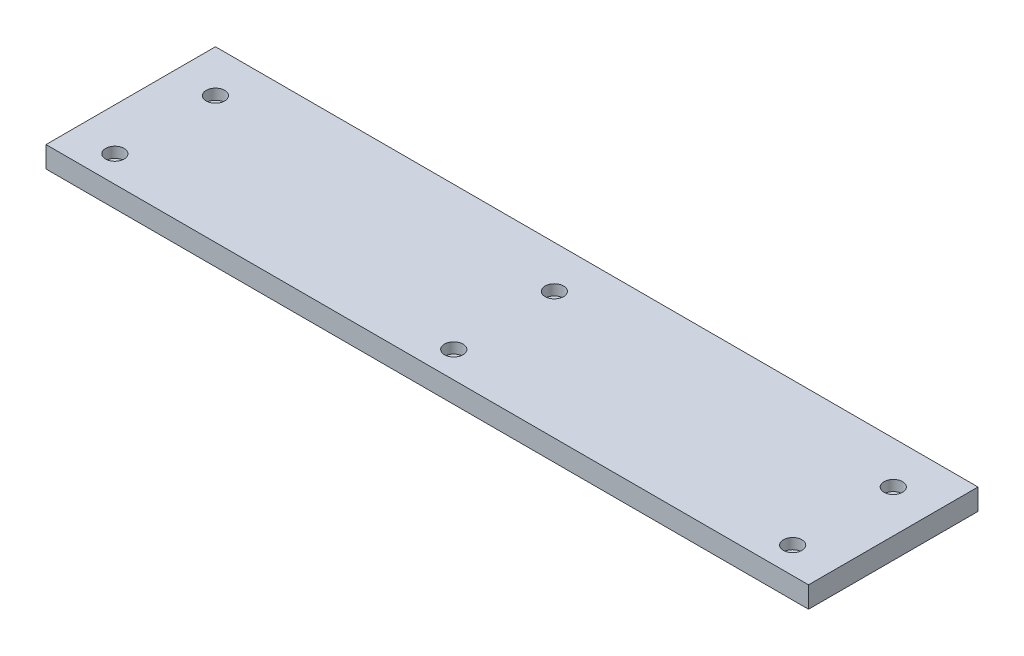
SolidWorks part; units mm, degrees
material "Ceramic Porcelain"
ref_plane "Front Plane" through (0, 0, 0) normal (0, 0, 1) x (1, 0, 0)
ref_plane "Top Plane" through (0, 0, 0) normal (0, 1, 0) x (1, 0, 0)
ref_plane "Right Plane" through (0, 0, 0) normal (1, 0, 0) x (0, 0, -1)
sketch "Sketch1" plane through (0, 0, 0) normal (0, 1, 0) x (1, 0, 0)
  line L1 (228.6, 50.8) -> (-228.6, 50.8)
  line L2 (228.6, 50.8) -> (228.6, -50.8)
  line L3 (228.6, -50.8) -> (-228.6, -50.8)
  line L4 (-228.6, 50.8) -> (-228.6, -50.8)
  line L5 (0, -50.8) -> (0, 50.8) construction
  line L6 (228.6, 0) -> (-228.6, 0) construction
  line L7 (203.2, -34.925) -> (-203.2, -34.925) construction
  line L8 (203.2, -34.925) -> (203.2, 25.4) construction
  line L9 (203.2, 25.4) -> (-203.2, 25.4) construction
  line L10 (-203.2, -34.925) -> (-203.2, 25.4) construction
  line L11 (0, 25.4) -> (0, -34.925) construction
  line L12 (203.2, -4.7625) -> (-203.2, -4.7625) construction
  point P0 (0, 0)
  point P4 (0, -4.7625)
  point P8 (0, 0)
  point P9 (0, 0)
  point P10 (0, 0)
  point P11 (0, 0)
  point P12 (0, 0)
  point P13 (0, 0)
  dimension "D1" = 101.6
  dimension "D2" = 457.2
  dimension "D3" = 25.4
  dimension "D4" = 60.325
  dimension "D5" = 25.4
extrude "Boss-Extrude1" add sketch "Sketch1" against normal blind 12.7
hole_wizard "CBORE for 1/4 Socket Head Cap Screw1" positions "Sketch2" profile "Sketch3" counterbore size "1/4" standard "ANSI Inch"
sketch "Sketch2" plane through (0, 0, 0) normal (0, 1, 0) x (1, 0, 0)
  point P4 (-203.2, 25.4)
  point P7 (-203.2, -34.925)
  point P10 (0, -34.925)
  point P13 (0, 25.4)
  point P16 (203.2, 25.4)
  point P19 (203.2, -34.925)
sketch "Sketch3" plane through (-203.2, 0, -25.4) normal (1, 0, 0) x (0, 0, 1)
  line L0 (0, 0) -> (0, 16.51)
  line L1 (0, 16.51) -> (3.3782, 14.4802)
  line L2 (3.3782, 14.4802) -> (3.3782, 6.35)
  line L3 (3.3782, 6.35) -> (5.5562, 6.35)
  line L4 (5.5562, 6.35) -> (5.5562, 0)
  line L5 (5.5562, 0) -> (0, 0)
  line L10 (0, 16.51) -> (-3.3782, 14.4802) construction
  line L11 (0, -6.35) -> (0, 107.95) construction
  dimension "Hole Dia." = 6.7564
  dimension "Hole Depth" = 16.51
  dimension "C'Bore Dia." = 11.1125
  dimension "C'Bore Depth" = 6.35
  dimension "Drill Angle" = 118
